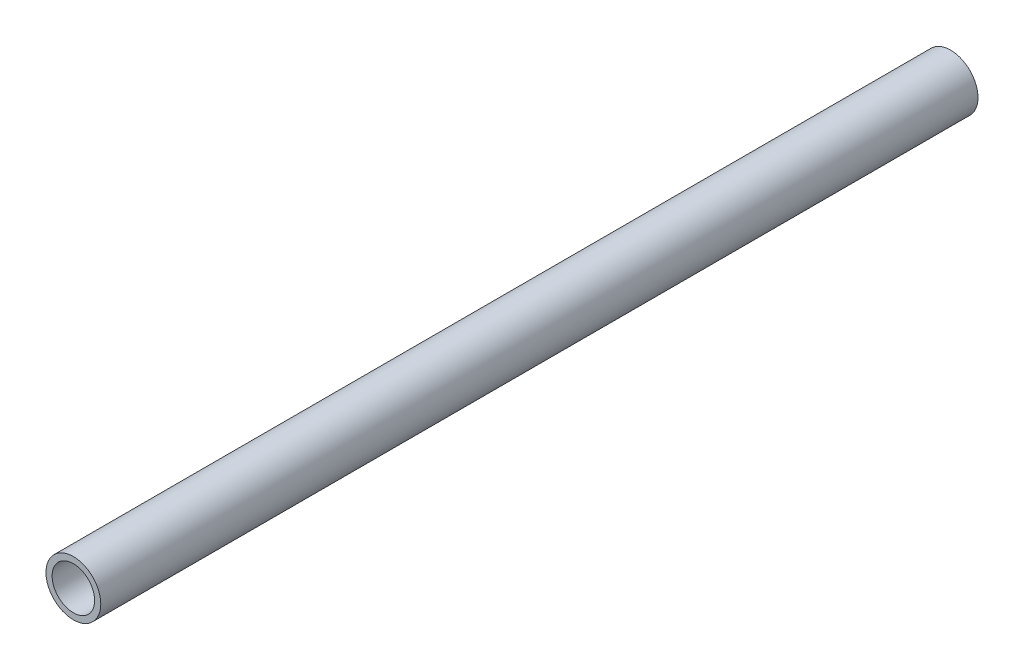
SolidWorks part; units mm, degrees
ref_plane "前视基准面" through (0, 0, 0) normal (0, 0, 1) x (1, 0, 0)
ref_plane "上视基准面" through (0, 0, 0) normal (0, 1, 0) x (1, 0, 0)
ref_plane "右视基准面" through (0, 0, 0) normal (1, 0, 0) x (0, 0, -1)
other "Configuration Table"
sketch "草图1" plane through (0, 0, 0) normal (0, 0, 1) x (1, 0, 0)
  circle A0 centre (0, 0) radius 12.5
  circle A1 centre (0, 0) radius 9.7
  dimension "D1" = 25
  dimension "D2" = 19.4
extrude "凸台-拉伸1" add sketch "草图1" along normal mid plane 400
